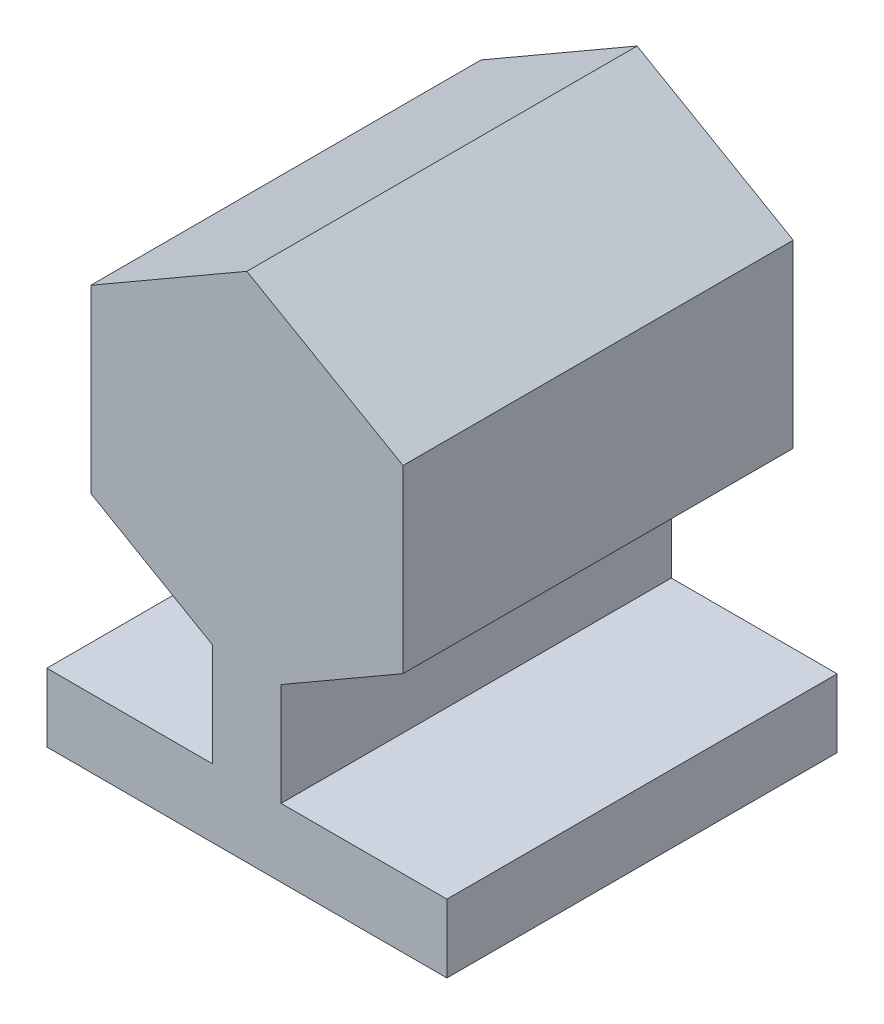
SolidWorks part; units mm, degrees
ref_plane "Front Plane" through (0, 0, 0) normal (0, 0, 1) x (1, 0, 0)
ref_plane "Top Plane" through (0, 0, 0) normal (0, 1, 0) x (1, 0, 0)
ref_plane "Right Plane" through (0, 0, 0) normal (1, 0, 0) x (0, 0, -1)
sketch "Sketch1" plane through (0, 0, 0) normal (0, 0, 1) x (1, 0, 0)
  line L0 (0, 0) -> (0, -170000) construction
  line L1 (0, 92376.0431) -> (-80000, 46188.0215)
  line L2 (-80000, 46188.0215) -> (-80000, -46188.0215)
  line L3 (-80000, -46188.0215) -> (-17500, -82272.4134)
  line L4 (17500, -82272.4134) -> (80000, -46188.0215)
  line L5 (80000, -46188.0215) -> (80000, 46188.0215)
  line L6 (80000, 46188.0215) -> (0, 92376.0431)
  line L7 (-102500, -170000) -> (102500, -170000)
  line L8 (102500, -170000) -> (102500, -135000)
  line L9 (-102500, -170000) -> (-102500, -135000)
  line L10 (102500, -135000) -> (17500, -135000)
  line L11 (17500, -135000) -> (17500, -82272.4134)
  line L12 (-102500, -135000) -> (-17500, -135000)
  line L13 (-17500, -135000) -> (-17500, -82272.4134)
  circle A0 centre (0, 0) radius 80000 construction
extrude "Boss-Extrude1" add sketch "Sketch1" along normal blind 200000
